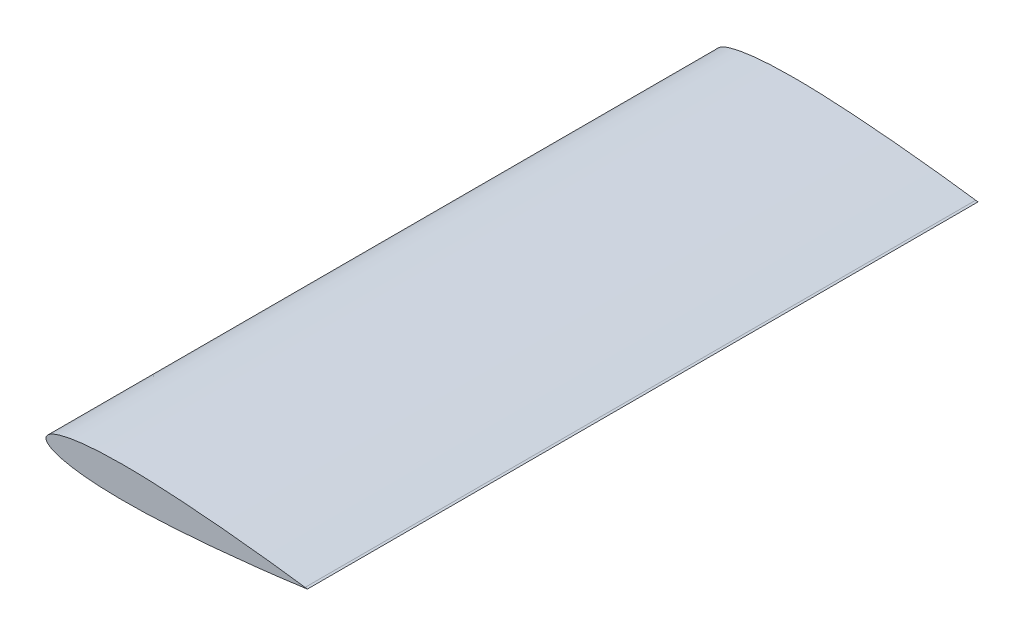
SolidWorks part; units mm, degrees
material "Default"
ref_plane "Front Plane" through (0, 0, 0) normal (0, 0, 1) x (1, 0, 0)
ref_plane "Top Plane" through (0, 0, 0) normal (0, 1, 0) x (1, 0, 0)
ref_plane "Right Plane" through (0, 0, 0) normal (1, 0, 0) x (0, 0, -1)
curve "Curve1"
  spline degree 3 poles (170, 0.2142, 0) (169.9669, 0.2188, 0) (169.8346, 0.2374, 0) (169.5373, 0.279, 0) (169.0426, 0.3481, 0) (168.3516, 0.4442, 0) (167.4659, 0.5667, 0) (166.3876, 0.7147, 0) (165.1192, 0.8874, 0) (163.6637, 1.0836, 0) (162.0245, 1.3022, 0) (160.2054, 1.5419, 0) (158.2106, 1.8012, 0) (156.0449, 2.0787, 0) (153.7132, 2.3729, 0) (151.2211, 2.6822, 0) (148.5743, 3.005, 0) (145.7789, 3.3395, 0) (142.8417, 3.6843, 0) (139.7694, 4.0375, 0) (136.5691, 4.3975, 0) (133.2484, 4.7626, 0) (129.815, 5.131, 0) (126.277, 5.501, 0) (122.6425, 5.8707, 0) (118.9201, 6.2384, 0) (115.1185, 6.6021, 0) (111.2466, 6.96, 0) (107.3134, 7.3101, 0) (103.328, 7.6504, 0) (99.2999, 7.9787, 0) (95.2383, 8.2931, 0) (91.1528, 8.5913, 0) (87.053, 8.8711, 0) (82.9484, 9.1303, 0) (78.8485, 9.3668, 0) (74.763, 9.5783, 0) (70.7014, 9.7627, 0) (66.6731, 9.9179, 0) (62.6877, 10.0419, 0) (58.7543, 10.1329, 0) (54.8822, 10.1892, 0) (51.0804, 10.2092, 0) (47.3578, 10.1916, 0) (43.7231, 10.1354, 0) (40.1848, 10.0398, 0) (36.751, 9.9041, 0) (33.4299, 9.7282, 0) (30.2292, 9.5119, 0) (27.1564, 9.2557, 0) (24.2185, 8.9602, 0) (21.4225, 8.6261, 0) (18.7748, 8.2547, 0) (16.2817, 7.8473, 0) (13.9488, 7.4054, 0) (11.7816, 6.9307, 0) (9.785, 6.4252, 0) (7.9635, 5.8907, 0) (6.3212, 5.3291, 0) (4.8614, 4.7425, 0) (3.5873, 4.1325, 0) (2.5009, 3.5004, 0) (1.6038, 2.8472, 0) (0.8975, 2.172, 0) (0.3842, 1.4725, 0) (0.07, 0.7458, 0) (-0.0341, 0, 0) (0.07, -0.7458, 0) (0.3842, -1.4725, 0) (0.8975, -2.172, 0) (1.6038, -2.8472, 0) (2.5009, -3.5004, 0) (3.5873, -4.1325, 0) (4.8614, -4.7425, 0) (6.3212, -5.3291, 0) (7.9635, -5.8907, 0) (9.785, -6.4252, 0) (11.7816, -6.9307, 0) (13.9488, -7.4054, 0) (16.2817, -7.8473, 0) (18.7748, -8.2547, 0) (21.4225, -8.6261, 0) (24.2185, -8.9602, 0) (27.1564, -9.2557, 0) (30.2292, -9.5119, 0) (33.4299, -9.7282, 0) (36.751, -9.9041, 0) (40.1848, -10.0398, 0) (43.7231, -10.1354, 0) (47.3578, -10.1916, 0) (51.0804, -10.2092, 0) (54.8822, -10.1892, 0) (58.7543, -10.1329, 0) (62.6877, -10.0419, 0) (66.6731, -9.9179, 0) (70.7014, -9.7627, 0) (74.763, -9.5783, 0) (78.8485, -9.3668, 0) (82.9484, -9.1303, 0) (87.053, -8.8711, 0) (91.1528, -8.5913, 0) (95.2383, -8.2931, 0) (99.2999, -7.9787, 0) (103.328, -7.6504, 0) (107.3134, -7.3101, 0) (111.2466, -6.96, 0) (115.1185, -6.6021, 0) (118.9201, -6.2384, 0) (122.6425, -5.8707, 0) (126.277, -5.501, 0) (129.815, -5.131, 0) (133.2484, -4.7626, 0) (136.5691, -4.3975, 0) (139.7694, -4.0375, 0) (142.8417, -3.6843, 0) (145.7789, -3.3395, 0) (148.5743, -3.005, 0) (151.2211, -2.6822, 0) (153.7132, -2.3729, 0) (156.0449, -2.0787, 0) (158.2106, -1.8012, 0) (160.2054, -1.5419, 0) (162.0245, -1.3022, 0) (163.6637, -1.0836, 0) (165.1192, -0.8874, 0) (166.3876, -0.7147, 0) (167.4659, -0.5667, 0) (168.3516, -0.4442, 0) (169.0426, -0.3481, 0) (169.5373, -0.279, 0) (169.8346, -0.2374, 0) (169.9669, -0.2188, 0) (170, -0.2142, 0) knots 0 0 0 0 0.000289 0.001156 0.002598 0.004612 0.007194 0.010336 0.014031 0.018271 0.023046 0.028343 0.03415 0.040454 0.047239 0.054489 0.062186 0.070314 0.078852 0.08778 0.097077 0.106722 0.116691 0.126961 0.137507 0.148306 0.159331 0.170557 0.181957 0.193504 0.205172 0.216932 0.228758 0.240621 0.252495 0.26435 0.276161 0.287898 0.299536 0.311047 0.322405 0.333584 0.344559 0.355306 0.3658 0.376018 0.385938 0.395538 0.404798 0.413699 0.422222 0.430349 0.438066 0.445357 0.452209 0.458611 0.464554 0.47003 0.475035 0.479569 0.483637 0.48725 0.490431 0.493219 0.495674 0.497891 0.5 0.502109 0.504326 0.506781 0.509569 0.51275 0.516363 0.520431 0.524965 0.52997 0.535446 0.541389 0.547791 0.554643 0.561934 0.569651 0.577778 0.586301 0.595202 0.604462 0.614062 0.623982 0.6342 0.644694 0.655441 0.666416 0.677595 0.688953 0.700464 0.712102 0.723839 0.73565 0.747505 0.759379 0.771242 0.783068 0.794828 0.806496 0.818043 0.829443 0.840669 0.851694 0.862493 0.873039 0.883309 0.893278 0.902923 0.91222 0.921148 0.929686 0.937814 0.945511 0.952761 0.959546 0.96585 0.971657 0.976954 0.981729 0.985969 0.989664 0.992806 0.995388 0.997402 0.998844 0.999711 1 1 1 1
sketch "Sketch1" plane through (0, 0, 0) normal (0, 0, 1) x (1, 0, 0)
  line L0 (170, 0.2142) -> (171.5269, 0)
  line L1 (170, -0.2142) -> (171.5269, 0)
  spline S0 degree 3 poles (842.9705, 3941.5127) (248.2307, -14.1528) (209.2013, -5.2739) (169.5373, 0.279) (169.0426, 0.3481) (168.3516, 0.4442) (167.4659, 0.5667) (166.3876, 0.7147) (165.1192, 0.8874) (163.6637, 1.0836) (162.0245, 1.3022) (160.2054, 1.5419) (158.2106, 1.8012) (156.0449, 2.0787) (153.7132, 2.3729) (151.2211, 2.6822) (148.5743, 3.005) (145.7789, 3.3395) (142.8417, 3.6843) (139.7694, 4.0375) (136.5691, 4.3975) (133.2484, 4.7626) (128.6033, 5.261) (123.8235, 5.754) (118.9201, 6.2384) (115.1185, 6.6021) (111.2466, 6.96) (107.3134, 7.3101) (103.328, 7.6504) (99.2999, 7.9787) (95.2383, 8.2931) (91.1528, 8.5913) (87.053, 8.8711) (82.9484, 9.1303) (78.8485, 9.3668) (74.763, 9.5783) (70.7014, 9.7627) (66.6731, 9.9179) (62.6877, 10.0419) (58.7543, 10.1329) (54.8822, 10.1892) (51.0804, 10.2092) (47.3578, 10.1916) (43.7231, 10.1354) (40.1848, 10.0398) (36.751, 9.9041) (33.4299, 9.7282) (30.2292, 9.5119) (27.1564, 9.2557) (24.2185, 8.9602) (21.4225, 8.6261) (18.7748, 8.2547) (16.2817, 7.8473) (13.9488, 7.4054) (11.7816, 6.9307) (9.785, 6.4252) (7.9635, 5.8907) (6.3212, 5.3291) (4.8614, 4.7425) (3.5873, 4.1325) (2.5009, 3.5004) (1.6038, 2.8472) (0.8975, 2.172) (0.3842, 1.4725) (0.07, 0.7458) (-0.0341, 0) (0.07, -0.7458) (0.3842, -1.4725) (0.8975, -2.172) (1.6038, -2.8472) (2.5009, -3.5004) (3.5873, -4.1325) (4.8614, -4.7425) (6.3212, -5.3291) (7.9635, -5.8907) (9.785, -6.4252) (11.7816, -6.9307) (13.9488, -7.4054) (16.2817, -7.8473) (18.7748, -8.2547) (21.4225, -8.6261) (24.2185, -8.9602) (27.1564, -9.2557) (30.2292, -9.5119) (33.4299, -9.7282) (36.751, -9.9041) (40.1848, -10.0398) (43.7231, -10.1354) (47.3578, -10.1916) (51.0804, -10.2092) (54.8822, -10.1892) (58.7543, -10.1329) (62.6877, -10.0419) (66.6731, -9.9179) (70.7014, -9.7627) (74.763, -9.5783) (78.8485, -9.3668) (82.9484, -9.1303) (87.053, -8.8711) (91.1528, -8.5913) (95.2383, -8.2931) (99.2999, -7.9787) (103.328, -7.6504) (107.3134, -7.3101) (111.2466, -6.96) (116.361, -6.4872) (122.5562, -5.8848) (128.6033, -5.261) (133.2484, -4.7626) (136.5691, -4.3975) (139.7694, -4.0375) (142.8417, -3.6843) (145.7789, -3.3395) (148.5743, -3.005) (151.2211, -2.6822) (153.7132, -2.3729) (156.0449, -2.0787) (158.2106, -1.8012) (160.2054, -1.5419) (162.0245, -1.3022) (163.6637, -1.0836) (165.1192, -0.8874) (166.3876, -0.7147) (167.4659, -0.5667) (168.3516, -0.4442) (169.0426, -0.3481) (169.5373, -0.279) (209.2001, 5.2737) (248.2283, 14.1522) (842.9141, -3941.1374) knots -0.344004 -0.344004 -0.344004 -0.344004 0.000289 0.001156 0.002598 0.004612 0.007194 0.010336 0.014031 0.018271 0.023046 0.028343 0.03415 0.040454 0.047239 0.054489 0.062186 0.070314 0.078852 0.08778 0.097077 0.106722 0.116691 0.137507 0.148306 0.159331 0.170557 0.181957 0.193504 0.205172 0.216932 0.228758 0.240621 0.252495 0.26435 0.276161 0.287898 0.299536 0.311047 0.322405 0.333584 0.344559 0.355306 0.3658 0.376018 0.385938 0.395538 0.404798 0.413699 0.422222 0.430349 0.438066 0.445357 0.452209 0.458611 0.464554 0.47003 0.475035 0.479569 0.483637 0.48725 0.490431 0.493219 0.495674 0.497891 0.5 0.502109 0.504326 0.506781 0.509569 0.51275 0.516363 0.520431 0.524965 0.52997 0.535446 0.541389 0.547791 0.554643 0.561934 0.569651 0.577778 0.586301 0.595202 0.604462 0.614062 0.623982 0.6342 0.644694 0.655441 0.666416 0.677595 0.688953 0.700464 0.712102 0.723839 0.73565 0.747505 0.759379 0.771242 0.783068 0.794828 0.806496 0.818043 0.829443 0.840669 0.862493 0.883309 0.893278 0.902923 0.91222 0.921148 0.929686 0.937814 0.945511 0.952761 0.959546 0.96585 0.971657 0.976954 0.981729 0.985969 0.989664 0.992806 0.995388 0.997402 0.998844 0.999711 1.343993 1.343993 1.343993 1.343993 only from (170, 0.2142) to (170, -0.2142) construction
  spline S1 degree 3 poles (170, 0.2142) (169.9669, 0.2188) (169.8346, 0.2374) (169.5373, 0.279) (169.0426, 0.3481) (168.3516, 0.4442) (167.4659, 0.5667) (166.3876, 0.7147) (165.1192, 0.8874) (163.6637, 1.0836) (162.0245, 1.3022) (160.2054, 1.5419) (158.2106, 1.8012) (156.0449, 2.0787) (153.7132, 2.3729) (151.2211, 2.6822) (148.5743, 3.005) (145.7789, 3.3395) (142.8417, 3.6843) (139.7694, 4.0375) (136.5691, 4.3975) (133.2484, 4.7626) (128.6033, 5.261) (123.8235, 5.754) (118.9201, 6.2384) (115.1185, 6.6021) (111.2466, 6.96) (107.3134, 7.3101) (103.328, 7.6504) (99.2999, 7.9787) (95.2383, 8.2931) (91.1528, 8.5913) (87.053, 8.8711) (82.9484, 9.1303) (78.8485, 9.3668) (74.763, 9.5783) (70.7014, 9.7627) (66.6731, 9.9179) (62.6877, 10.0419) (58.7543, 10.1329) (54.8822, 10.1892) (51.0804, 10.2092) (47.3578, 10.1916) (43.7231, 10.1354) (40.1848, 10.0398) (36.751, 9.9041) (33.4299, 9.7282) (30.2292, 9.5119) (27.1564, 9.2557) (24.2185, 8.9602) (21.4225, 8.6261) (18.7748, 8.2547) (16.2817, 7.8473) (13.9488, 7.4054) (11.7816, 6.9307) (9.785, 6.4252) (7.9635, 5.8907) (6.3212, 5.3291) (4.8614, 4.7425) (3.5873, 4.1325) (2.5009, 3.5004) (1.6038, 2.8472) (0.8975, 2.172) (0.3842, 1.4725) (0.07, 0.7458) (-0.0341, 0) (0.07, -0.7458) (0.3842, -1.4725) (0.8975, -2.172) (1.6038, -2.8472) (2.5009, -3.5004) (3.5873, -4.1325) (4.8614, -4.7425) (6.3212, -5.3291) (7.9635, -5.8907) (9.785, -6.4252) (11.7816, -6.9307) (13.9488, -7.4054) (16.2817, -7.8473) (18.7748, -8.2547) (21.4225, -8.6261) (24.2185, -8.9602) (27.1564, -9.2557) (30.2292, -9.5119) (33.4299, -9.7282) (36.751, -9.9041) (40.1848, -10.0398) (43.7231, -10.1354) (47.3578, -10.1916) (51.0804, -10.2092) (54.8822, -10.1892) (58.7543, -10.1329) (62.6877, -10.0419) (66.6731, -9.9179) (70.7014, -9.7627) (74.763, -9.5783) (78.8485, -9.3668) (82.9484, -9.1303) (87.053, -8.8711) (91.1528, -8.5913) (95.2383, -8.2931) (99.2999, -7.9787) (103.328, -7.6504) (107.3134, -7.3101) (111.2466, -6.96) (116.361, -6.4872) (122.5562, -5.8848) (128.6033, -5.261) (133.2484, -4.7626) (136.5691, -4.3975) (139.7694, -4.0375) (142.8417, -3.6843) (145.7789, -3.3395) (148.5743, -3.005) (151.2211, -2.6822) (153.7132, -2.3729) (156.0449, -2.0787) (158.2106, -1.8012) (160.2054, -1.5419) (162.0245, -1.3022) (163.6637, -1.0836) (165.1192, -0.8874) (166.3876, -0.7147) (167.4659, -0.5667) (168.3516, -0.4442) (169.0426, -0.3481) (169.5373, -0.279) (169.8346, -0.2374) (169.9669, -0.2188) (170, -0.2142) knots 0 0 0 0 0.000289 0.001156 0.002598 0.004612 0.007194 0.010336 0.014031 0.018271 0.023046 0.028343 0.03415 0.040454 0.047239 0.054489 0.062186 0.070314 0.078852 0.08778 0.097077 0.106722 0.116691 0.137507 0.148306 0.159331 0.170557 0.181957 0.193504 0.205172 0.216932 0.228758 0.240621 0.252495 0.26435 0.276161 0.287898 0.299536 0.311047 0.322405 0.333584 0.344559 0.355306 0.3658 0.376018 0.385938 0.395538 0.404798 0.413699 0.422222 0.430349 0.438066 0.445357 0.452209 0.458611 0.464554 0.47003 0.475035 0.479569 0.483637 0.48725 0.490431 0.493219 0.495674 0.497891 0.5 0.502109 0.504326 0.506781 0.509569 0.51275 0.516363 0.520431 0.524965 0.52997 0.535446 0.541389 0.547791 0.554643 0.561934 0.569651 0.577778 0.586301 0.595202 0.604462 0.614062 0.623982 0.6342 0.644694 0.655441 0.666416 0.677595 0.688953 0.700464 0.712102 0.723839 0.73565 0.747505 0.759379 0.771242 0.783068 0.794828 0.806496 0.818043 0.829443 0.840669 0.862493 0.883309 0.893278 0.902923 0.91222 0.921148 0.929686 0.937814 0.945511 0.952761 0.959546 0.96585 0.971657 0.976954 0.981729 0.985969 0.989664 0.992806 0.995388 0.997402 0.998844 0.999711 1 1 1 1
extrude "Boss-Extrude1" add sketch "Sketch1" along normal mid plane 440
